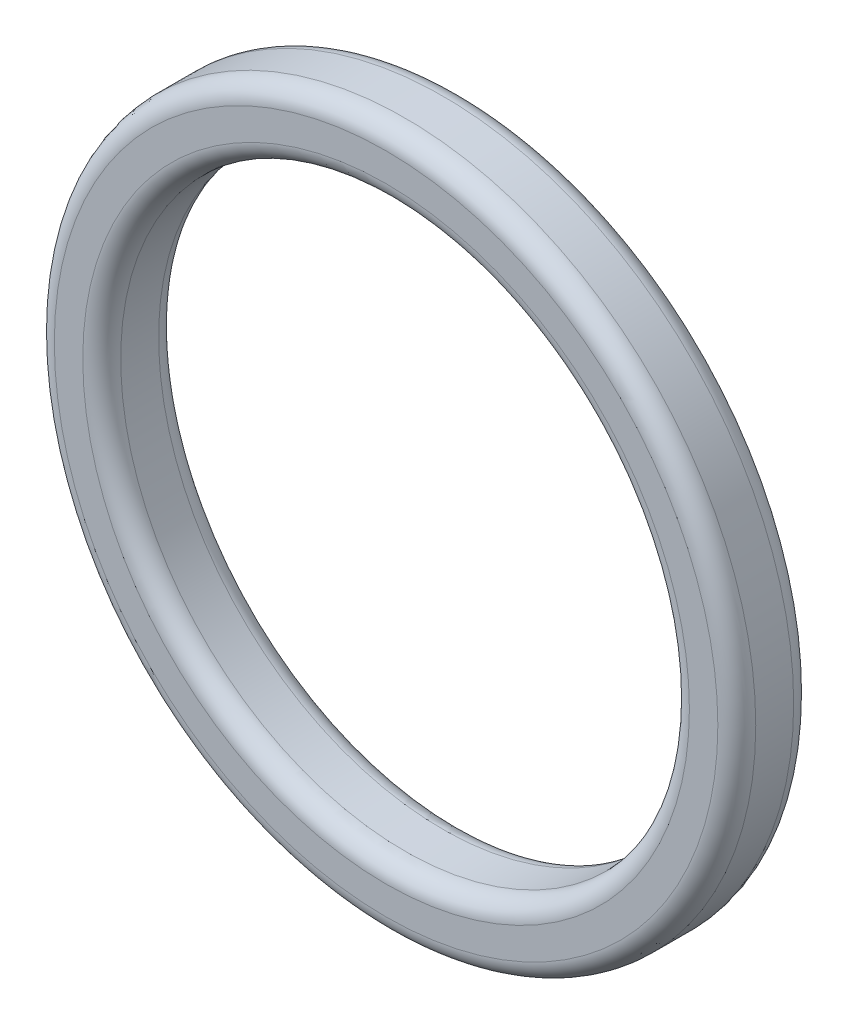
SolidWorks part; units mm, degrees
ref_plane "前视基准面" through (0, 0, 0) normal (0, 0, 1) x (1, 0, 0)
ref_plane "上视基准面" through (0, 0, 0) normal (0, 1, 0) x (1, 0, 0)
ref_plane "右视基准面" through (0, 0, 0) normal (1, 0, 0) x (0, 0, -1)
sketch "草图1" plane through (0, 0, 0) normal (0, 0, 1) x (1, 0, 0)
  circle A0 centre (0, 0) radius 18.5
  circle A1 centre (0, 0) radius 15
  dimension "D1" = 30
  dimension "D2" = 37
extrude "凸台-拉伸1" add sketch "草图1" along normal blind 4
fillet "圆角1" radius 1 4 edges at (15, 0, 4) (18.5, 0, 0) (18.5, 0, 4) (15, 0, 0)
